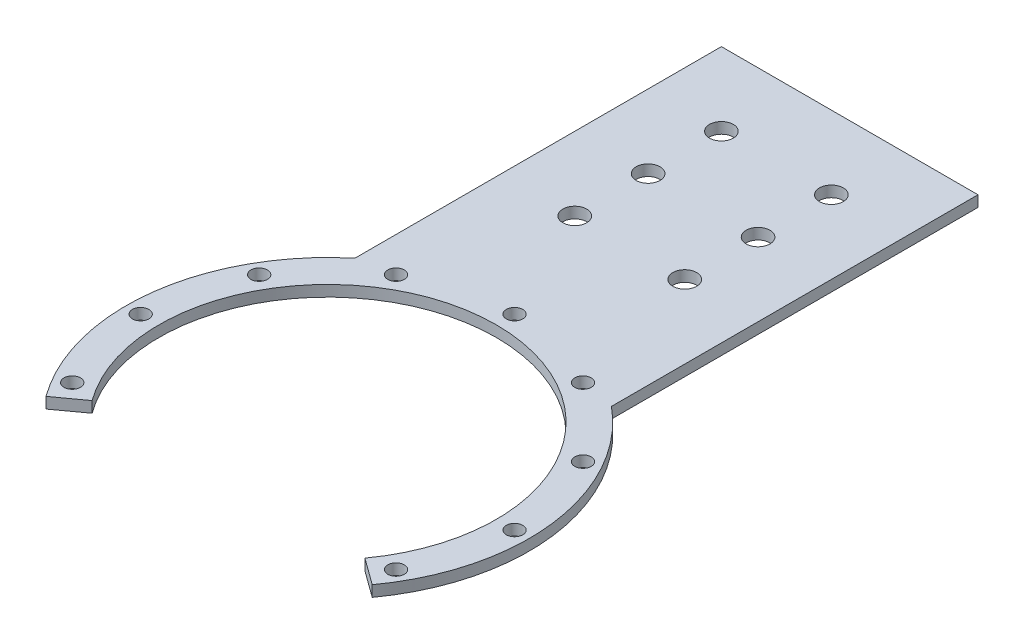
SolidWorks part; units mm, degrees
ref_plane "Front Plane" through (0, 0, 0) normal (0, 0, 1) x (1, 0, 0)
ref_plane "Top Plane" through (0, 0, 0) normal (0, 1, 0) x (1, 0, 0)
ref_plane "Right Plane" through (0, 0, 0) normal (1, 0, 0) x (0, 0, -1)
sketch "Sketch1" plane through (0, 0, 0) normal (0, 1, 0) x (1, 0, 0)
  circle A0 centre (0, 0) radius 55
  dimension "D1" = 110
extrude "Boss-Extrude1" add sketch "Sketch1" along normal blind 3
sketch "Sketch2" plane through (0, 0, 0) normal (0, 1, 0) x (1, 0, 0)
  line L0 (0, 0) -> (0, 92.4264) construction
  line L1 (-35, 142.4264) -> (-35, 42.4264)
  line L2 (-35, 142.4264) -> (35, 142.4264)
  line L3 (-35, 42.4264) -> (35, 42.4264)
  line L4 (35, 142.4264) -> (35, 42.4264)
  line L5 (0, 42.4264) -> (0, 142.4264) construction
  line L6 (-35, 92.4264) -> (35, 92.4264) construction
  circle A0 centre (0, 0) radius 55 construction
  dimension "D1" = 100
  dimension "D2" = 70
extrude "Boss-Extrude2" add sketch "Sketch2" along normal blind 3
sketch "Sketch4" plane through (0, 3, 0) normal (0, 1, 0) x (1, 0, 0)
  circle A0 centre (0, 0) radius 51 construction
  circle A1 centre (0, 0) radius 46
  dimension "D1" = 102
  dimension "D2" = 92
extrude "Cut-Extrude2" cut sketch "Sketch4" against normal through all both and the other way through all
sketch "Sketch7" plane through (0, 3, 0) normal (0, 1, 0) x (1, 0, 0)
  line L0 (0, 0) -> (0, -55)
  line L1 (0, 0) -> (-44.4959, -32.3282)
  arc A0 (-35, 42.4264) -> (35, 42.4264) centre (0, 0) ccw construction
  arc A1 (0, -55) -> (-44.4959, -32.3282) centre (0, 0) cw
  dimension "D1" = 54
extrude "Cut-Extrude5" cut sketch "Sketch7" against normal through all both and the other way through all
mirror "Mirror1" about plane through (0, 0, 0) normal (1, 0, 0) of "Cut-Extrude5"
sketch "Sketch5" plane through (0, 3, 0) normal (0, 1, 0) x (1, 0, 0)
  circle A0 centre (0, 0) radius 51 construction
  circle A1 centre (0, 51) radius 2.25
  dimension "D1" = 102
  dimension "D2" = 4.5
extrude "Cut-Extrude3" cut sketch "Sketch5" against normal through all both and the other way through all
pattern_circular "CirPattern1" count 12 over 360 about axis through (0, 0, 0) along (0, 1, 0) of "Cut-Extrude3"
sketch "Sketch6" plane through (0, 3, 0) normal (0, 1, 0) x (1, 0, 0)
  line L0 (0, 142.4264) -> (0, 0) construction
  line L1 (35, 142.4264) -> (-35, 142.4264) construction
  line L2 (-15, 122.4264) -> (15, 122.4264) construction
  circle A0 centre (15, 122.4264) radius 3.25
  circle A1 centre (-15, 122.4264) radius 3.25
  point P8 (0, 122.4264)
  dimension "D1" = 6.5
  dimension "D2" = 30
  dimension "D3" = 20
extrude "Cut-Extrude4" cut sketch "Sketch6" against normal through all both and the other way through all
pattern_linear "LPattern1" count 3 spacing 20 along (0, 0, 1) of "Cut-Extrude4"
